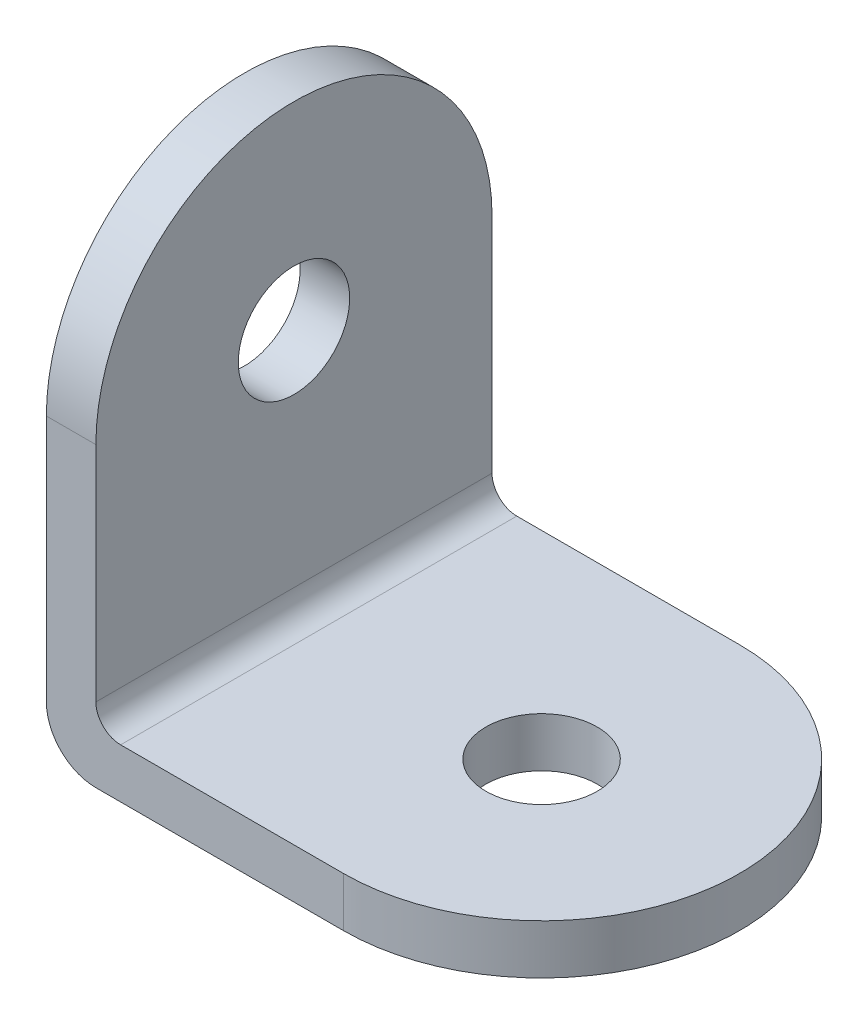
SolidWorks part; units mm, degrees
material "Литая легированная сталь"
ref_plane "Спереди" through (0, 0, 0) normal (0, 0, 1) x (1, 0, 0)
ref_plane "Сверху" through (0, 0, 0) normal (0, 1, 0) x (1, 0, 0)
ref_plane "Справа" through (0, 0, 0) normal (1, 0, 0) x (0, 0, -1)
sketch "Эскиз1" plane through (0, 0, 0) normal (0, 0, 1) x (1, 0, 0)
  line L0 (0, 0) -> (0, 20)
  line L1 (0, 20) -> (2, 20)
  line L2 (2, 20) -> (2, 2)
  line L3 (2, 2) -> (20, 2)
  line L4 (20, 2) -> (20, 0)
  line L5 (20, 0) -> (0, 0)
  dimension "D1" = 2
  dimension "D2" = 20
extrude "Бобышка-Вытянуть1" add sketch "Эскиз1" along normal blind 16
sketch "Эскиз2" plane through (0, 0, 0) normal (0, -1, 0) x (1, 0, 0)
  line L0 (20, 8) -> (0, 8) construction
  line L3 (20, 16) -> (20, 0) construction
  line L4 (0, 16) -> (0, 0) construction
  line L5 (0, 16) -> (20, 16) construction
  line L6 (0, 0) -> (20, 0) construction
  line L7 (12, 16) -> (20, 16)
  line L8 (20, 16) -> (20, 0)
  line L9 (12, 0) -> (20, 0)
  arc A0 (12, 0) -> (12, 16) centre (12, 8) ccw
  line M5 (0, 0) -> (20, 0)
  line M6 (20, 0) -> (20, 16)
  line M7 (20, 16) -> (0, 16)
extrude "Вырез-Вытянуть1" cut sketch "Эскиз2" against normal through all contours A0 M5 M6 | A0 L8 M7
sketch "Эскиз3" plane through (0, 0, 0) normal (-1, 0, 0) x (0, 0, 1)
  line L0 (8, 20) -> (8, 0) construction
  line L1 (16, 20) -> (0, 20) construction
  line L2 (16, 0) -> (0, 0) construction
  line L3 (0, 20) -> (0, 0) construction
  line L8 (0, 20) -> (0, 0)
  line L9 (0, 0) -> (16, 0)
  line L10 (16, 0) -> (16, 20)
  line L11 (16, 20) -> (0, 20)
  line L12 (0, 20) -> (0, 12)
  line L14 (16, 12) -> (16, 20)
  line L15 (16, 20) -> (0, 20)
  arc A0 (16, 12) -> (0, 12) centre (8, 12) ccw
  line M5 (0, 20) -> (0, 0)
  line M7 (16, 0) -> (16, 20)
  line M8 (16, 20) -> (0, 20)
  dimension "D1" = 0
extrude "Вырез-Вытянуть2" cut sketch "Эскиз3" against normal through all contours A0 L15 M5 | A0 M7 M8
fillet "Скругление1" radius 1 1 edges at (2, 2, 8)
fillet "Скругление2" radius 2 1 edges at (0, 0, 8)
sketch "Эскиз4" plane through (2, 0, 0) normal (1, 0, 0) x (0, 0, -1)
  line L0 (-8, 20) -> (-8, 12) construction
  arc A0 (0, 12) -> (-16, 12) centre (-8, 12) ccw construction
  circle A1 centre (-8, 12) radius 2.25
  dimension "D1" = 4.5
extrude "Вырез-Вытянуть3" cut sketch "Эскиз4" against normal through all
sketch "Эскиз5" plane through (0, 2, 0) normal (0, 1, 0) x (1, 0, 0)
  line L0 (20, -8) -> (12, -8) construction
  arc A0 (12, -16) -> (12, 0) centre (12, -8) ccw construction
  circle A1 centre (12, -8) radius 2.25
  dimension "D1" = 4.5
extrude "Вырез-Вытянуть4" cut sketch "Эскиз5" against normal through all
sketch "Эскиз 1" plane through (0, 0, 0) normal (-1, 0, 0) x (0, 0, 1)
  line L0 (8, 20) -> (8, 2) construction
  line L1 (0, 2) -> (16, 2) construction
  arc A0 (16, 12) -> (0, 12) centre (8, 12) ccw construction
ref_plane "S" through (0, 0, 8) normal (0, 0, -1) x (0, -1, 0)
